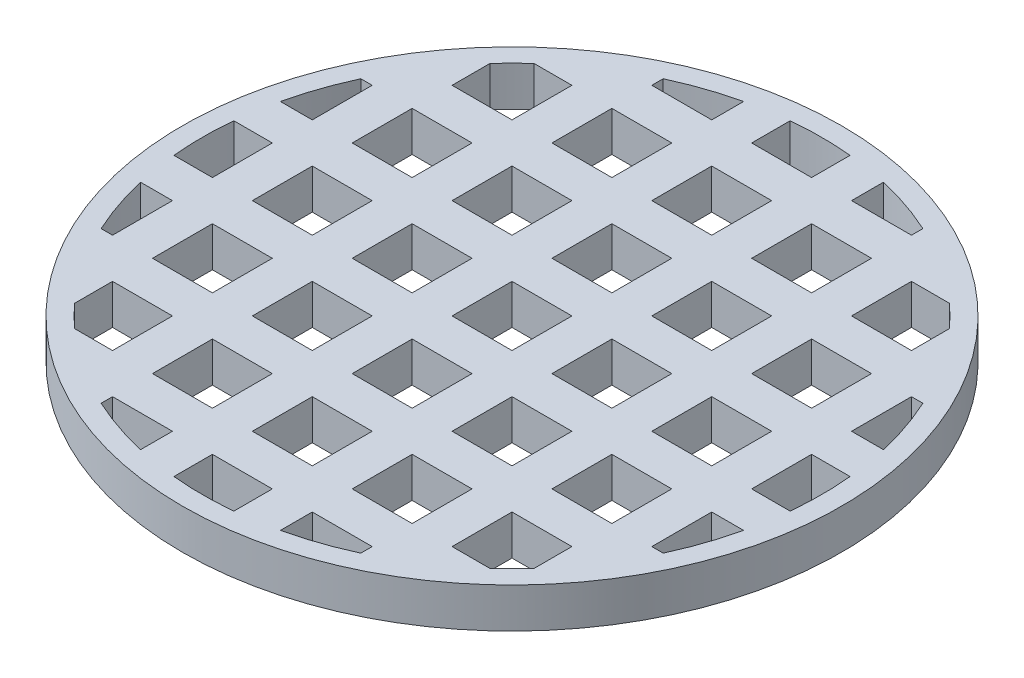
SolidWorks part; units mm, degrees
ref_plane "Front Plane" through (0, 0, 0) normal (0, 0, 1) x (1, 0, 0)
ref_plane "Top Plane" through (0, 0, 0) normal (0, 1, 0) x (1, 0, 0)
ref_plane "Right Plane" through (0, 0, 0) normal (1, 0, 0) x (0, 0, -1)
sketch "Sketch1" plane through (0, 0, 0) normal (0, 1, 0) x (1, 0, 0)
  line L0 (3.5, 1.5) -> (3.5, -1.5)
  line L1 (-1.5, 1.5) -> (1.5, 1.5)
  line L2 (-1.5, 1.5) -> (-1.5, -1.5)
  line L3 (-1.5, -1.5) -> (1.5, -1.5)
  line L4 (1.5, 1.5) -> (1.5, -1.5)
  line L5 (3.5, 1.5) -> (6.5, 1.5)
  line L6 (6.5, 1.5) -> (6.5, -1.5)
  line L7 (3.5, -1.5) -> (6.5, -1.5)
  line L8 (8.5, 1.5) -> (8.5, -1.5)
  line L9 (8.5, 1.5) -> (11.5, 1.5)
  line L10 (11.5, 1.5) -> (11.5, -1.5)
  line L11 (8.5, -1.5) -> (11.5, -1.5)
  line L12 (13.5, 1.5) -> (13.5, -1.5)
  line L13 (13.5, 1.5) -> (16.5, 1.5)
  line L14 (16.5, 1.5) -> (16.5, -1.5)
  line L15 (13.5, -1.5) -> (16.5, -1.5)
  line L16 (3.5, 6.5) -> (3.5, 3.5)
  line L17 (3.5, 6.5) -> (6.5, 6.5)
  line L18 (6.5, 6.5) -> (6.5, 3.5)
  line L19 (3.5, 3.5) -> (6.5, 3.5)
  line L20 (8.5, 6.5) -> (8.5, 3.5)
  line L21 (8.5, 6.5) -> (11.5, 6.5)
  line L22 (11.5, 6.5) -> (11.5, 3.5)
  line L23 (8.5, 3.5) -> (11.5, 3.5)
  line L24 (13.5, 6.5) -> (13.5, 3.5)
  line L25 (13.5, 6.5) -> (16.5, 6.5)
  line L26 (16.5, 6.5) -> (16.5, 3.5)
  line L27 (13.5, 3.5) -> (16.5, 3.5)
  line L28 (3.5, 11.5) -> (3.5, 8.5)
  line L29 (3.5, 11.5) -> (6.5, 11.5)
  line L30 (6.5, 11.5) -> (6.5, 8.5)
  line L31 (3.5, 8.5) -> (6.5, 8.5)
  line L32 (8.5, 11.5) -> (8.5, 8.5)
  line L33 (8.5, 11.5) -> (11.5, 11.5)
  line L34 (11.5, 11.5) -> (11.5, 8.5)
  line L35 (8.5, 8.5) -> (11.5, 8.5)
  line L36 (13.5, 11.5) -> (13.5, 8.5)
  line L37 (13.5, 11.5) -> (16.5, 11.5)
  line L38 (16.5, 11.5) -> (16.5, 8.5)
  line L39 (13.5, 8.5) -> (16.5, 8.5)
  line L40 (3.5, 16.5) -> (3.5, 13.5)
  line L41 (3.5, 16.5) -> (6.5, 16.5)
  line L42 (6.5, 16.5) -> (6.5, 13.5)
  line L43 (3.5, 13.5) -> (6.5, 13.5)
  line L44 (8.5, 16.5) -> (8.5, 13.5)
  line L45 (8.5, 16.5) -> (11.5, 16.5)
  line L46 (11.5, 16.5) -> (11.5, 13.5)
  line L47 (8.5, 13.5) -> (11.5, 13.5)
  line L48 (13.5, 16.5) -> (13.5, 13.5)
  line L49 (13.5, 16.5) -> (16.5, 16.5)
  line L50 (16.5, 16.5) -> (16.5, 13.5)
  line L51 (13.5, 13.5) -> (16.5, 13.5)
  line L52 (-1.5, 6.5) -> (-1.5, 3.5)
  line L53 (-1.5, 6.5) -> (1.5, 6.5)
  line L54 (1.5, 6.5) -> (1.5, 3.5)
  line L55 (-1.5, 3.5) -> (1.5, 3.5)
  line L56 (-1.5, 11.5) -> (-1.5, 8.5)
  line L57 (-1.5, 11.5) -> (1.5, 11.5)
  line L58 (1.5, 11.5) -> (1.5, 8.5)
  line L59 (-1.5, 8.5) -> (1.5, 8.5)
  line L60 (-1.5, 16.5) -> (-1.5, 13.5)
  line L61 (-1.5, 16.5) -> (1.5, 16.5)
  line L62 (1.5, 16.5) -> (1.5, 13.5)
  line L63 (-1.5, 13.5) -> (1.5, 13.5)
  line L64 (0, -55) -> (0, 55) construction
  line L65 (-8.5, 16.5) -> (-11.5, 16.5)
  line L66 (-11.5, 16.5) -> (-11.5, 13.5)
  line L67 (-8.5, 13.5) -> (-11.5, 13.5)
  line L68 (-8.5, 16.5) -> (-8.5, 13.5)
  line L69 (-3.5, 16.5) -> (-6.5, 16.5)
  line L70 (-6.5, 16.5) -> (-6.5, 13.5)
  line L71 (-3.5, 13.5) -> (-6.5, 13.5)
  line L72 (-3.5, 16.5) -> (-3.5, 13.5)
  line L73 (-8.5, 11.5) -> (-11.5, 11.5)
  line L74 (-11.5, 11.5) -> (-11.5, 8.5)
  line L75 (-8.5, 8.5) -> (-11.5, 8.5)
  line L76 (-8.5, 11.5) -> (-8.5, 8.5)
  line L77 (-3.5, 11.5) -> (-6.5, 11.5)
  line L78 (-6.5, 11.5) -> (-6.5, 8.5)
  line L79 (-3.5, 8.5) -> (-6.5, 8.5)
  line L80 (-3.5, 11.5) -> (-3.5, 8.5)
  line L81 (-13.5, 6.5) -> (-16.5, 6.5)
  line L82 (-16.5, 6.5) -> (-16.5, 3.5)
  line L83 (-13.5, 3.5) -> (-16.5, 3.5)
  line L84 (-13.5, 6.5) -> (-13.5, 3.5)
  line L85 (-8.5, 6.5) -> (-11.5, 6.5)
  line L86 (-11.5, 6.5) -> (-11.5, 3.5)
  line L87 (-8.5, 3.5) -> (-11.5, 3.5)
  line L88 (-8.5, 6.5) -> (-8.5, 3.5)
  line L89 (-3.5, 6.5) -> (-6.5, 6.5)
  line L90 (-6.5, 6.5) -> (-6.5, 3.5)
  line L91 (-3.5, 3.5) -> (-6.5, 3.5)
  line L92 (-3.5, 6.5) -> (-3.5, 3.5)
  line L93 (-13.5, 1.5) -> (-16.5, 1.5)
  line L94 (-16.5, 1.5) -> (-16.5, -1.5)
  line L95 (-13.5, -1.5) -> (-16.5, -1.5)
  line L96 (-13.5, 1.5) -> (-13.5, -1.5)
  line L97 (-8.5, 1.5) -> (-11.5, 1.5)
  line L98 (-11.5, 1.5) -> (-11.5, -1.5)
  line L99 (-8.5, -1.5) -> (-11.5, -1.5)
  line L100 (-8.5, 1.5) -> (-8.5, -1.5)
  line L101 (-3.5, 1.5) -> (-6.5, 1.5)
  line L102 (-6.5, 1.5) -> (-6.5, -1.5)
  line L103 (-3.5, -1.5) -> (-6.5, -1.5)
  line L104 (-3.5, 1.5) -> (-3.5, -1.5)
  line L105 (-55, 0) -> (55, 0) construction
  line L106 (-3.5, 1.5) -> (-6.5, 1.5)
  line L107 (-3.5, -1.5) -> (-6.5, -1.5)
  line L108 (-8.5, 1.5) -> (-11.5, 1.5)
  line L109 (-8.5, -1.5) -> (-11.5, -1.5)
  line L110 (-13.5, 1.5) -> (-16.5, 1.5)
  line L111 (-13.5, -1.5) -> (-16.5, -1.5)
  line L112 (-3.5, -6.5) -> (-3.5, -3.5)
  line L113 (-3.5, -3.5) -> (-6.5, -3.5)
  line L114 (-6.5, -6.5) -> (-6.5, -3.5)
  line L115 (-3.5, -6.5) -> (-6.5, -6.5)
  line L116 (-8.5, -6.5) -> (-8.5, -3.5)
  line L117 (-8.5, -3.5) -> (-11.5, -3.5)
  line L118 (-11.5, -6.5) -> (-11.5, -3.5)
  line L119 (-8.5, -6.5) -> (-11.5, -6.5)
  line L120 (-13.5, -6.5) -> (-13.5, -3.5)
  line L121 (-13.5, -3.5) -> (-16.5, -3.5)
  line L122 (-16.5, -6.5) -> (-16.5, -3.5)
  line L123 (-13.5, -6.5) -> (-16.5, -6.5)
  line L124 (-3.5, -11.5) -> (-3.5, -8.5)
  line L125 (-3.5, -8.5) -> (-6.5, -8.5)
  line L126 (-6.5, -11.5) -> (-6.5, -8.5)
  line L127 (-3.5, -11.5) -> (-6.5, -11.5)
  line L128 (-8.5, -11.5) -> (-8.5, -8.5)
  line L129 (-8.5, -8.5) -> (-11.5, -8.5)
  line L130 (-11.5, -11.5) -> (-11.5, -8.5)
  line L131 (-8.5, -11.5) -> (-11.5, -11.5)
  line L132 (-3.5, -16.5) -> (-3.5, -13.5)
  line L133 (-3.5, -13.5) -> (-6.5, -13.5)
  line L134 (-6.5, -16.5) -> (-6.5, -13.5)
  line L135 (-3.5, -16.5) -> (-6.5, -16.5)
  line L136 (-8.5, -16.5) -> (-8.5, -13.5)
  line L137 (-8.5, -13.5) -> (-11.5, -13.5)
  line L138 (-11.5, -16.5) -> (-11.5, -13.5)
  line L139 (-8.5, -16.5) -> (-11.5, -16.5)
  line L140 (-1.5, -13.5) -> (1.5, -13.5)
  line L141 (1.5, -16.5) -> (1.5, -13.5)
  line L142 (-1.5, -16.5) -> (1.5, -16.5)
  line L143 (-1.5, -16.5) -> (-1.5, -13.5)
  line L144 (-1.5, -8.5) -> (1.5, -8.5)
  line L145 (1.5, -11.5) -> (1.5, -8.5)
  line L146 (-1.5, -11.5) -> (1.5, -11.5)
  line L147 (-1.5, -11.5) -> (-1.5, -8.5)
  line L148 (-1.5, -3.5) -> (1.5, -3.5)
  line L149 (1.5, -6.5) -> (1.5, -3.5)
  line L150 (-1.5, -6.5) -> (1.5, -6.5)
  line L151 (-1.5, -6.5) -> (-1.5, -3.5)
  line L152 (13.5, -13.5) -> (16.5, -13.5)
  line L153 (16.5, -16.5) -> (16.5, -13.5)
  line L154 (13.5, -16.5) -> (16.5, -16.5)
  line L155 (13.5, -16.5) -> (13.5, -13.5)
  line L156 (8.5, -13.5) -> (11.5, -13.5)
  line L157 (11.5, -16.5) -> (11.5, -13.5)
  line L158 (8.5, -16.5) -> (11.5, -16.5)
  line L159 (8.5, -16.5) -> (8.5, -13.5)
  line L160 (3.5, -13.5) -> (6.5, -13.5)
  line L161 (6.5, -16.5) -> (6.5, -13.5)
  line L162 (3.5, -16.5) -> (6.5, -16.5)
  line L163 (3.5, -16.5) -> (3.5, -13.5)
  line L164 (13.5, -8.5) -> (16.5, -8.5)
  line L165 (16.5, -11.5) -> (16.5, -8.5)
  line L166 (13.5, -11.5) -> (16.5, -11.5)
  line L167 (13.5, -11.5) -> (13.5, -8.5)
  line L168 (8.5, -8.5) -> (11.5, -8.5)
  line L169 (11.5, -11.5) -> (11.5, -8.5)
  line L170 (8.5, -11.5) -> (11.5, -11.5)
  line L171 (8.5, -11.5) -> (8.5, -8.5)
  line L172 (3.5, -8.5) -> (6.5, -8.5)
  line L173 (6.5, -11.5) -> (6.5, -8.5)
  line L174 (3.5, -11.5) -> (6.5, -11.5)
  line L175 (3.5, -11.5) -> (3.5, -8.5)
  line L176 (13.5, -3.5) -> (16.5, -3.5)
  line L177 (16.5, -6.5) -> (16.5, -3.5)
  line L178 (13.5, -6.5) -> (16.5, -6.5)
  line L179 (13.5, -6.5) -> (13.5, -3.5)
  line L180 (8.5, -3.5) -> (11.5, -3.5)
  line L181 (11.5, -6.5) -> (11.5, -3.5)
  line L182 (8.5, -6.5) -> (11.5, -6.5)
  line L183 (8.5, -6.5) -> (8.5, -3.5)
  line L184 (3.5, -3.5) -> (6.5, -3.5)
  line L185 (6.5, -6.5) -> (6.5, -3.5)
  line L186 (3.5, -6.5) -> (6.5, -6.5)
  line L187 (3.5, -6.5) -> (3.5, -3.5)
  line L188 (13.5, 1.5) -> (16.5, 1.5)
  line L189 (13.5, -1.5) -> (16.5, -1.5)
  line L190 (8.5, 1.5) -> (11.5, 1.5)
  line L191 (8.5, -1.5) -> (11.5, -1.5)
  line L192 (3.5, 1.5) -> (6.5, 1.5)
  line L193 (3.5, -1.5) -> (6.5, -1.5)
  line L194 (-1.5, 1.5) -> (1.5, 1.5)
  line L195 (-1.5, -1.5) -> (1.5, -1.5)
  circle A0 centre (0, 0) radius 16.5
  point P8 (1.5, 0)
  point P9 (0, -1.5)
  dimension "D1" = 33
  dimension "D2" = 3
  dimension "D3" = 4
  dimension "D4" = 4
extrude "Boss-Extrude1" add sketch "Sketch1" along normal blind 2 contours L141 A0 L163 L160 L161 L159 L156 L167 L164 L178 L179 L176 L15 L12 L13 L27 L24 L25 L39 L36 L47 L44 L42 L43 L40 L62 L63 L60 L72 L71 L70 L68 L67 L81 L84 L83 L93 L96
sketch "Sketch2" plane through (0, 2, 0) normal (0, 1, 0) x (1, 0, 0)
  circle A0 centre (0, 0) radius 16.5
  circle A1 centre (0, 0) radius 15.5
  dimension "D1" = 1
extrude "Boss-Extrude2" add sketch "Sketch2" against normal blind 2
